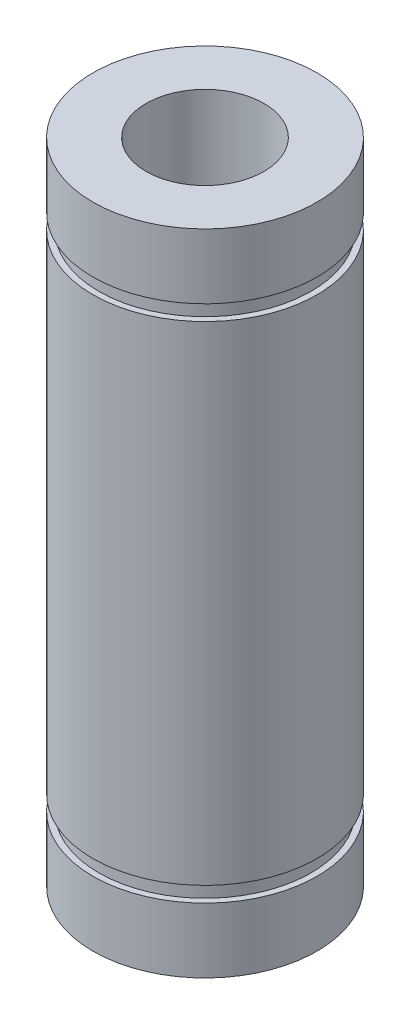
SolidWorks part; units mm, degrees
ref_plane "Front Plane" through (0, 0, 0) normal (0, 0, 1) x (1, 0, 0)
ref_plane "Top Plane" through (0, 0, 0) normal (0, 1, 0) x (1, 0, 0)
ref_plane "Right Plane" through (0, 0, 0) normal (1, 0, 0) x (0, 0, -1)
sketch "Sketch1" plane through (0, 0, 0) normal (0, 0, 1) x (1, 0, 0)
  line L0 (0, 46.0446) -> (0, -45.4182) construction
  line L1 (0, 0) -> (13.2112, 0) construction
  line L2 (5, 27.5) -> (9.5, 27.5)
  line L3 (5, 27.5) -> (5, -27.5)
  line L4 (5, -27.5) -> (9.5, -27.5)
  line L5 (9.5, 27.5) -> (9.5, 22)
  line L6 (9.5, 20.7) -> (9.5, -20.7)
  line L7 (9.5, 22) -> (9, 22)
  line L8 (9.5, -22) -> (9.5, -27.5)
  line L9 (9.5, 20.7) -> (9, 20.7)
  line L10 (9, 22) -> (9, 20.7)
  line L11 (9.5, -20.7) -> (9, -20.7)
  line L13 (9.5, -22) -> (9, -22)
  line L14 (9, -20.7) -> (9, -22)
  dimension "D1" = 10
  dimension "D2" = 19
  dimension "D3" = 55
  dimension "D4" = 44
  dimension "D5" = 1.3
  dimension "D6" = 1.3
  dimension "D7" = 18
revolve "Revolve1" add sketch "Sketch1" angle 360 about L0
equation "\"D6@Sketch1\"=\"D5@Sketch1\""
